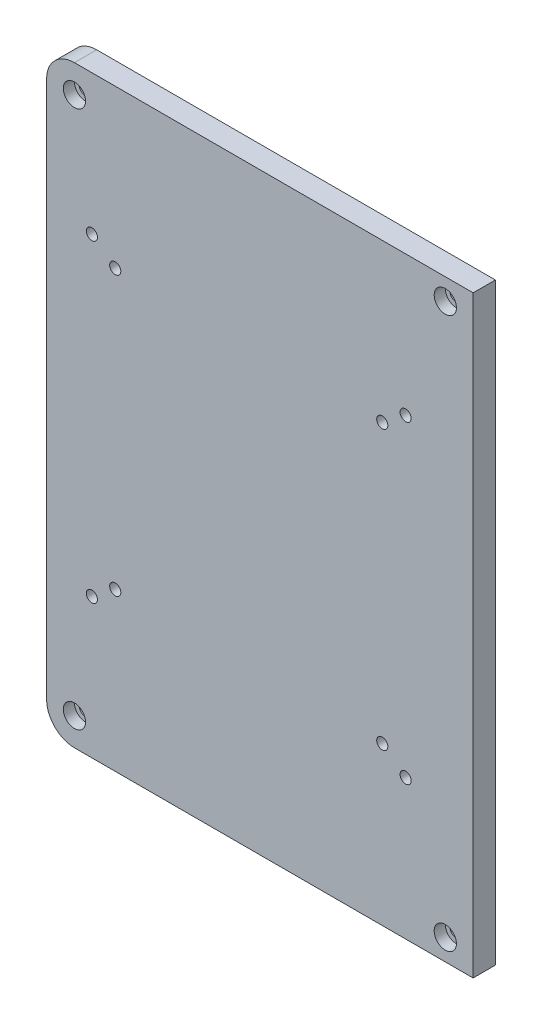
SolidWorks part; units mm, degrees
ref_plane "Front Plane" through (0, 0, 0) normal (0, 0, 1) x (1, 0, 0)
ref_plane "Top Plane" through (0, 0, 0) normal (0, 1, 0) x (1, 0, 0)
ref_plane "Right Plane" through (0, 0, 0) normal (1, 0, 0) x (0, 0, -1)
sketch "Sketch1" plane through (0, 0, 0) normal (0, 0, 1) x (1, 0, 0)
  line L1 (-107.5, 80) -> (107.5, 80)
  line L2 (-115, 72.5) -> (-115, -72.5)
  line L3 (-107.5, -80) -> (107.5, -80)
  line L4 (115, 72.5) -> (115, -72.5)
  line L5 (-115, 80) -> (115, -80) construction
  line L6 (-115, -80) -> (115, 80) construction
  arc A0 (-115, -72.5) -> (-107.5, -80) centre (-107.5, -72.5) ccw
  arc A1 (107.5, -80) -> (115, -72.5) centre (107.5, -72.5) ccw
  arc A2 (107.5, 80) -> (115, 72.5) centre (107.5, 72.5) cw
  arc A3 (-107.5, 80) -> (-115, 72.5) centre (-107.5, 72.5) ccw
  point P0 (0, 0)
  dimension "D3" = 7.5
  dimension "D1" = 230
  dimension "D2" = 160
extrude "Boss-Extrude1" add sketch "Sketch1" along normal blind 6
sketch "Sketch2" plane through (0, 0, 6) normal (0, 0, 1) x (1, 0, 0)
  line L0 (-115, 72.5) -> (-115, -72.5) construction
  line L1 (-107.5, -80) -> (107.5, -80) construction
  line L2 (107.5, 80) -> (-107.5, 80) construction
  line L3 (115, -72.5) -> (115, 72.5) construction
  circle A0 centre (-107.5, -72.5) radius 1.75
  circle A1 centre (-107.5, 72.5) radius 1.75
  circle A2 centre (107.5, -72.5) radius 1.75
  circle A3 centre (107.5, 72.5) radius 1.75
  dimension "D1" = 7.5
  dimension "D3" = 3.5
  dimension "D4" = 3.5
  dimension "D7" = 3.5
  dimension "D10" = 3.5
  dimension "D2" = 7.5
  dimension "D5" = 7.5
  dimension "D6" = 7.5
  dimension "D8" = 7.5
  dimension "D9" = 7.5
  dimension "D11" = 7.5
  dimension "D12" = 7.5
extrude "Cut-Extrude1" cut sketch "Sketch2" against normal blind 10
sketch "Sketch4" plane through (0, 0, 6) normal (0, 0, 1) x (1, 0, 0)
  line L0 (107.5, 80) -> (-107.5, 80) construction
  line L3 (-115, 72.5) -> (-115, -72.5) construction
  line L4 (-107.5, -80) -> (107.5, -80) construction
  circle A0 centre (-96.5, 37.5) radius 1.5
  circle A1 centre (-96.5, -37.5) radius 1.5
  circle A2 centre (-24.5, 37.5) radius 1.5
  circle A3 centre (-24.5, -37.5) radius 1.5
  dimension "D2" = 3
  dimension "D3" = 3
  dimension "D6" = 3
  dimension "D7" = 3
  dimension "D1" = 75
  dimension "D4" = 42.5
  dimension "D5" = 18.5
  dimension "D8" = 72
  dimension "D9" = 72
  dimension "D10" = 42.5
  dimension "D11" = 42.5
extrude "Cut-Extrude3" cut sketch "Sketch4" against normal through all
sketch "Sketch5" plane through (0, 0, 6) normal (0, 0, 1) x (1, 0, 0)
  line L0 (-107.5, -80) -> (107.5, -80) construction
  line L2 (115, -72.5) -> (115, 72.5) construction
  circle A0 centre (95, -62.5) radius 1.375
  circle A1 centre (95, 62.5) radius 1.375
  circle A2 centre (41.7, -62.5) radius 1.375
  circle A3 centre (41.7, 62.5) radius 1.375
  dimension "D1" = 125
  dimension "D4" = 2.75
  dimension "D6" = 53.3
  dimension "D2" = 17.5
  dimension "D3" = 20
  dimension "D5" = 53.3
extrude "Cut-Extrude4" cut sketch "Sketch5" against normal through all and the other way through all
sketch "Sketch7" plane through (0, 0, 6) normal (0, 0, 1) x (1, 0, 0)
  circle A0 centre (-102.8, 42.3) radius 1.5
  circle A1 centre (-96.5, 37.5) radius 1.5 construction
  circle A2 centre (-102.8, -42.3) radius 1.5
  circle A3 centre (-18.2, -42.3) radius 1.5
  circle A4 centre (-18.2, 42.3) radius 1.5
  circle A5 centre (-96.5, -37.5) radius 1.5 construction
  circle A6 centre (-24.5, -37.5) radius 1.5 construction
  circle A7 centre (-24.5, 37.5) radius 1.5 construction
  dimension "D1" = 6.3
  dimension "D3" = 3
  dimension "D4" = 3
  dimension "D5" = 3
  dimension "D6" = 3
  dimension "D7" = 4.8
  dimension "D8" = 6.3
  dimension "D10" = 4.8
  dimension "D11" = 4.8
  dimension "D12" = 6.3
  dimension "D2" = 4.8
extrude "Cut-Extrude6" cut sketch "Sketch7" against normal through all
sketch "Sketch9" plane through (0, 0, 6) normal (0, 0, 1) x (1, 0, 0)
  line L0 (115, -72.5) -> (115, 72.5) construction
  line L1 (0, 80) -> (115, 80)
  line L2 (0, 80) -> (0, -80)
  line L3 (0, -80) -> (115, -80)
  line L4 (115, 80) -> (115, -80)
  line L5 (107.5, 80) -> (-107.5, 80) construction
  line L6 (-107.5, -80) -> (107.5, -80) construction
  line L7 (-115, 72.5) -> (-115, -72.5) construction
  dimension "D1" = 0
  dimension "D2" = 0
  dimension "D3" = 0
  dimension "D4" = 115
extrude "Cut-Extrude8" cut sketch "Sketch9" against normal blind 10
sketch "Sketch10" plane through (0, 0, 6) normal (0, 0, 1) x (1, 0, 0)
  line L0 (0, 80) -> (0, -80) construction
  line L1 (-107.5, -80) -> (0, -80) construction
  circle A0 centre (-7.5, -74.25) radius 1.75
  dimension "D1" = 3.5
  dimension "D2" = 7.5
  dimension "D3" = 5.75
extrude "Cut-Extrude9" cut sketch "Sketch10" against normal up to surface (6 mm away) up to face at (-101.3, -42.3, 0)
sketch "Sketch16" plane through (0, 0, 6) normal (0, 0, 1) x (1, 0, 0)
  line L0 (0, 80) -> (-107.5, 80) construction
  line L1 (0, 80) -> (0, -80) construction
  circle A0 centre (-7.5, 74.25) radius 1.75
  dimension "D3" = 3.5
  dimension "D1" = 5.75
  dimension "D2" = 7.5
extrude "Cut-Extrude11" cut sketch "Sketch16" against normal up to surface (6 mm away) up to face at (-5.75, -74.25, 0)
sketch "Sketch19" plane through (0, 0, 6) normal (0, 0, 1) x (1, 0, 0)
  circle A0 centre (-107.5, -72.5) radius 3
  circle A1 centre (-7.5, -74.25) radius 3
  circle A2 centre (-7.5, 74.25) radius 3
  circle A3 centre (-107.5, 72.5) radius 3
  dimension "D1" = 6
  dimension "D2" = 6
  dimension "D3" = 6
  dimension "D4" = 6
extrude "Cut-Extrude13" cut sketch "Sketch19" against normal blind 3
